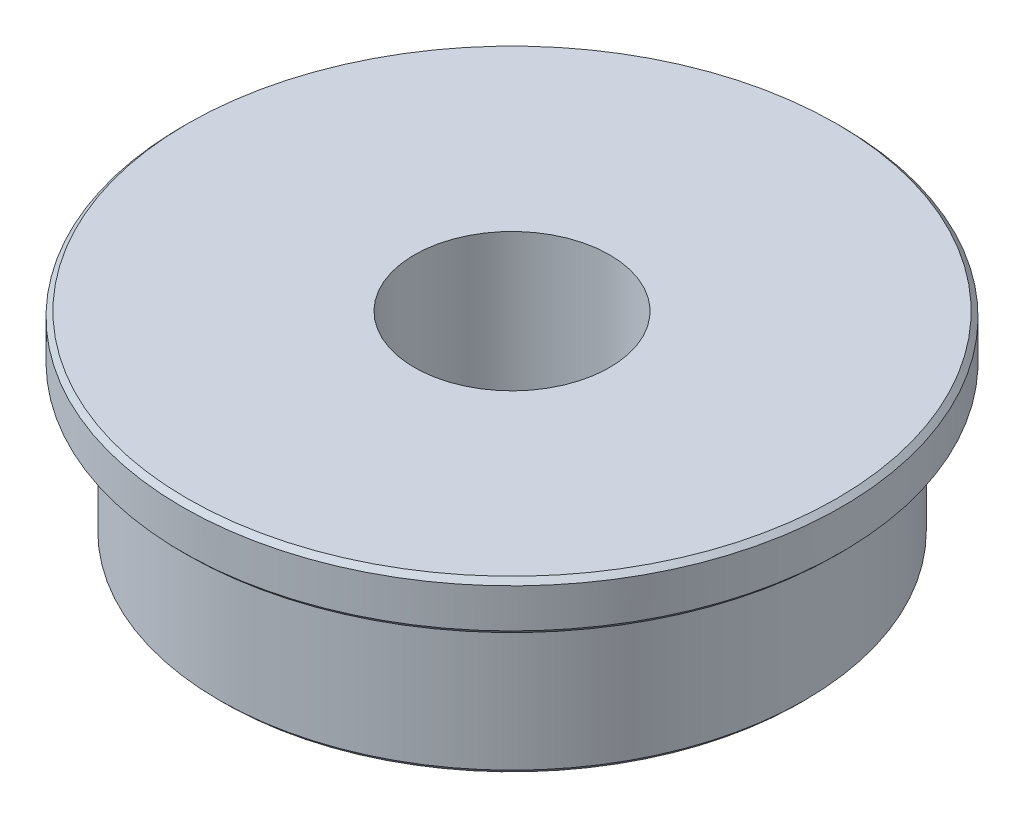
SolidWorks part; units mm, degrees
material "1060 合金"
ref_plane "前视基准面" through (0, 0, 0) normal (0, 0, 1) x (1, 0, 0)
ref_plane "上视基准面" through (0, 0, 0) normal (0, 1, 0) x (1, 0, 0)
ref_plane "右视基准面" through (0, 0, 0) normal (1, 0, 0) x (0, 0, -1)
sketch "草图1" plane through (0, 0, 0) normal (0, 0, 1) x (1, 0, 0)
  line L0 (0, 0) -> (0, 4.7757) construction
  line L1 (2, 0) -> (2, 4)
  line L2 (2, 4) -> (6.75, 4)
  line L3 (6.75, 4) -> (6.75, 3)
  line L4 (6.75, 3) -> (6, 3)
  line L5 (6, 3) -> (6, 0)
  line L6 (6, 0) -> (2, 0)
  dimension "D1" = 1
  dimension "D2" = 2
  dimension "D3" = 12
  dimension "D4" = 4
  dimension "D5" = 13.5
revolve "旋转1" add sketch "草图1" angle 360 about L0
chamfer "倒角1" distance 0.1 angle 45 3 edges at (0, 0, -6) (0, 3, -6.75) (0, 4, -6.75)
